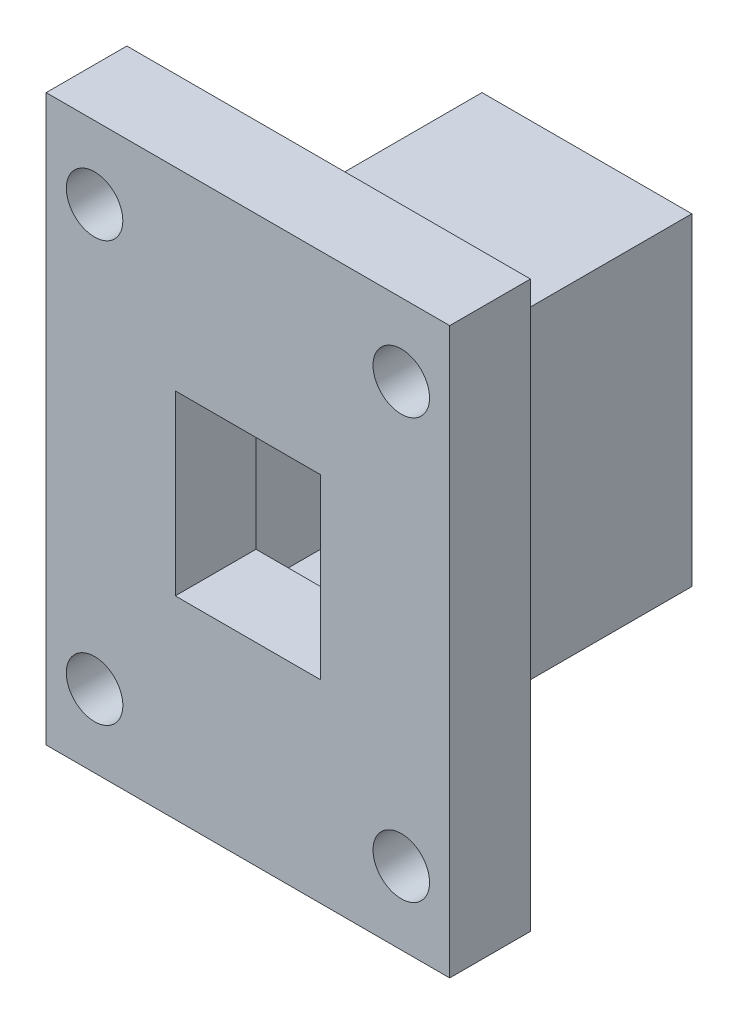
SolidWorks part; units mm, degrees
ref_plane "Front Plane" through (0, 0, 0) normal (0, 0, 1) x (1, 0, 0)
ref_plane "Top Plane" through (0, 0, 0) normal (0, 1, 0) x (1, 0, 0)
ref_plane "Right Plane" through (0, 0, 0) normal (1, 0, 0) x (0, 0, -1)
sketch "Sketch1" plane through (0, 0, 0) normal (0, 0, 1) x (1, 0, 0)
  line L1 (0, 0) -> (25, 0)
  line L2 (0, 0) -> (0, 35)
  line L3 (0, 35) -> (25, 35)
  line L4 (25, 0) -> (25, 35)
  dimension "D1" = 35
  dimension "D2" = 25
extrude "Boss-Extrude1" add sketch "Sketch1" along normal blind 5
sketch "Sketch2" plane through (0, 0, 5) normal (0, 0, 1) x (1, 0, 0)
  line L0 (25, 35) -> (0, 35) construction
  line L1 (8, 23) -> (17, 23)
  line L2 (8, 23) -> (8, 12)
  line L3 (8, 12) -> (17, 12)
  line L4 (17, 23) -> (17, 12)
  line L5 (25, 0) -> (25, 35) construction
  point P4 (12.5, 23)
  point P7 (12.5, 35)
  point P8 (17, 17.5)
  point P11 (25, 17.5)
  dimension "D1" = 9
  dimension "D2" = 11
extrude "Cut-Extrude1" cut sketch "Sketch2" against normal through all
sketch "Sketch3" plane through (0, 0, 5) normal (0, 0, 1) x (1, 0, 0)
  line L0 (12.5, 35) -> (12.5, 23.958) construction
  line L1 (25, 35) -> (0, 35) construction
  line L2 (0, 17.5) -> (12.5, 17.5) construction
  line L3 (0, 35) -> (0, 0) construction
  circle A0 centre (3, 30.5) radius 1.75
  circle A1 centre (3, 4.5) radius 1.75
  circle A2 centre (22, 4.5) radius 1.75
  circle A3 centre (22, 30.5) radius 1.75
  dimension "D1" = 3.5
  dimension "D2" = 26
  dimension "D3" = 19
extrude "Cut-Extrude2" cut sketch "Sketch3" against normal through all
sketch "Sketch4" plane through (0, 0, 0) normal (0, 0, -1) x (-1, 0, 0)
  line L0 (-25, 0) -> (-25, 35) construction
  line L1 (-17.5, 25.5) -> (-7.5, 25.5)
  line L2 (-17.5, 25.5) -> (-17.5, 9.5)
  line L3 (-17.5, 9.5) -> (-7.5, 9.5)
  line L4 (-7.5, 25.5) -> (-7.5, 9.5)
  line L5 (-19, 27.5) -> (-6, 27.5)
  line L6 (-19, 27.5) -> (-19, 7.5)
  line L7 (-19, 7.5) -> (-6, 7.5)
  line L8 (-6, 27.5) -> (-6, 7.5)
  line L9 (0, 0) -> (-25, 0) construction
  point P8 (-17.5, 17.5)
  point P11 (-25, 17.5)
  point P12 (-19, 17.5)
  point P13 (-12.5, 9.5)
  point P16 (-12.5, 0)
  point P17 (-12.5, 7.5)
  dimension "D1" = 16
  dimension "D2" = 10
  dimension "D3" = 20
  dimension "D4" = 13
extrude "Boss-Extrude2" add sketch "Sketch4" along normal blind 16
